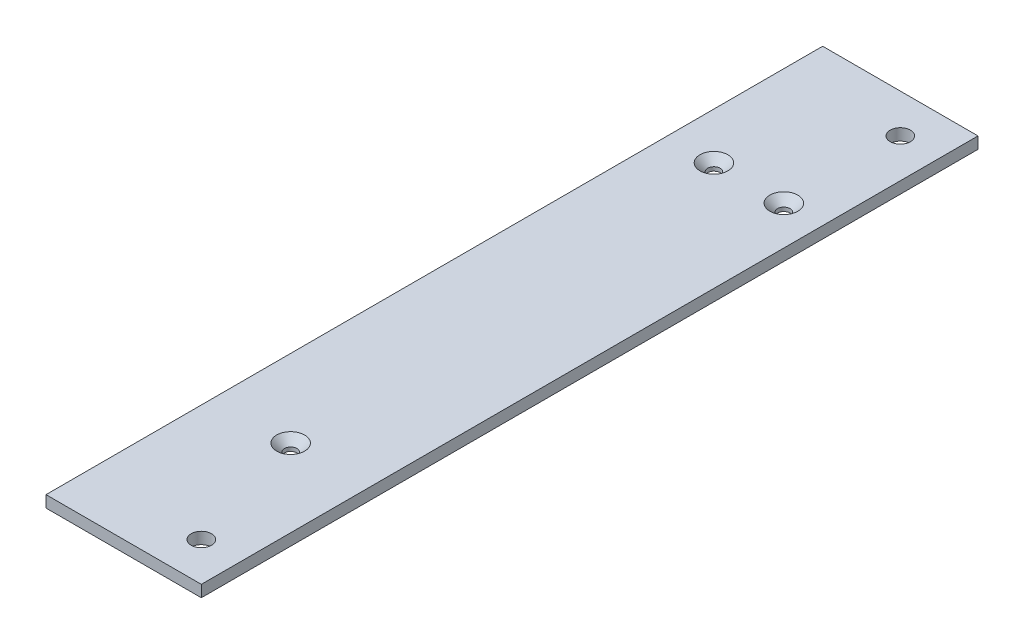
SolidWorks part; units mm, degrees
ref_plane "Front Plane" through (0, 0, 0) normal (0, 0, 1) x (1, 0, 0)
ref_plane "Top Plane" through (0, 0, 0) normal (0, 1, 0) x (1, 0, 0)
ref_plane "Right Plane" through (0, 0, 0) normal (1, 0, 0) x (0, 0, -1)
sketch "Sketch1" plane through (0, 0, 0) normal (0, 1, 0) x (1, 0, 0)
  line L0 (0, 100) -> (0, -100) construction
  line L1 (-20, -100) -> (20, -100)
  line L2 (-20, -100) -> (-20, 100)
  line L3 (-20, 100) -> (20, 100)
  line L4 (20, -100) -> (20, 100)
  line L5 (-20, -100) -> (20, 100) construction
  line L6 (-20, 100) -> (20, -100) construction
  line L7 (20, 60) -> (-20, 60) construction
  line L8 (10, 100) -> (10, -100) construction
  circle A0 centre (10, -90) radius 2.6
  circle A1 centre (10, 90) radius 2.6
  circle A2 centre (10, 60) radius 1.6
  circle A3 centre (-8, 60) radius 1.6
  circle A4 centre (0, -57) radius 1.6
  point P0 (0, 0)
  point P22 (0, 0)
  point P23 (5.7117, -90)
  point P24 (0, 0)
  point P25 (0, 0)
  point P26 (5.1362, 90)
  dimension "D3" = 5.2
  dimension "D4" = 5.2
  dimension "D6" = 10
  dimension "D7" = 3.2
  dimension "D8" = 3.2
  dimension "D9" = 10
  dimension "D12" = 3.2
  dimension "D1" = 40
  dimension "D2" = 200
  dimension "D5" = 10
  dimension "D10" = 18
  dimension "D11" = 40
  dimension "D13" = 117
extrude "Boss-Extrude1" add sketch "Sketch1" along normal blind 3
chamfer "Chamfer1" distance 2 angle 45 3 edges at (0, 3, 58.6) (-8, 3, -58.4) (10, 3, -58.4)
